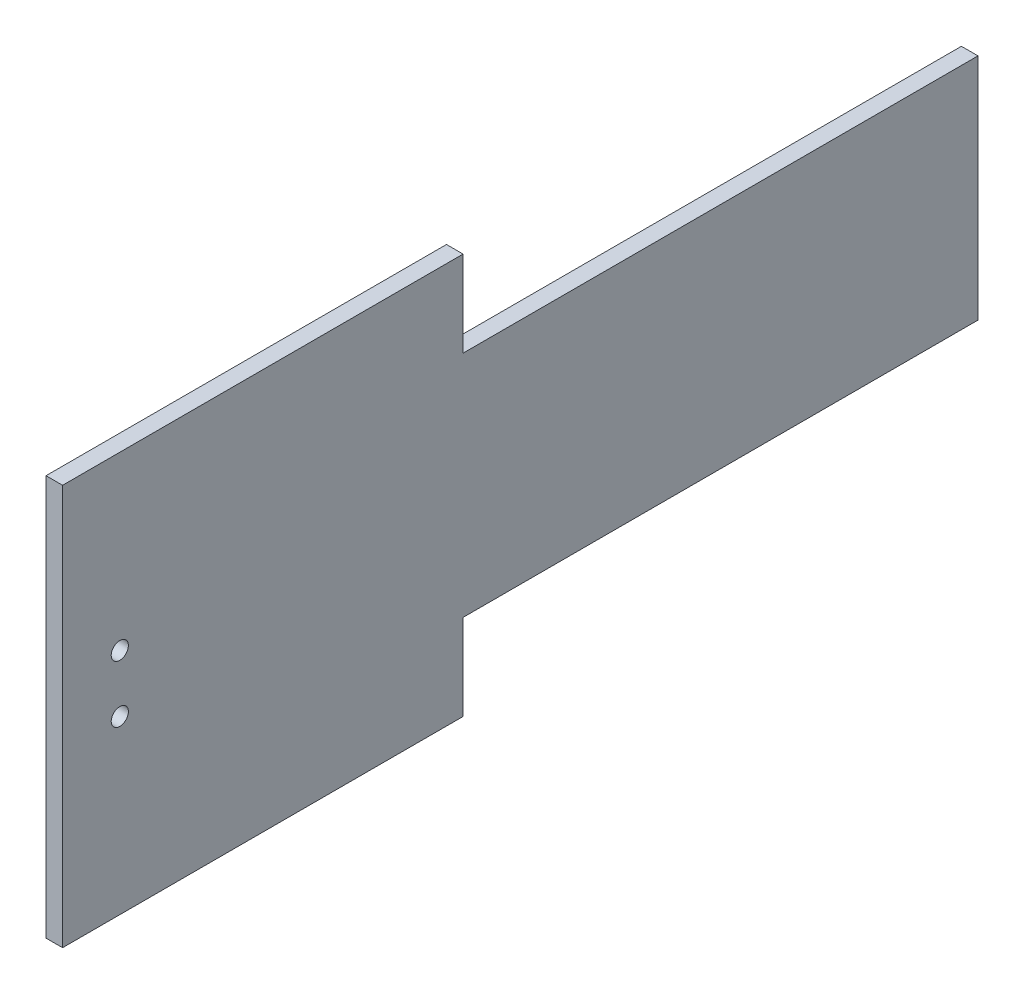
SolidWorks part; units mm, degrees
ref_plane "Front Plane" through (0, 0, 0) normal (0, 0, 1) x (1, 0, 0)
ref_plane "Top Plane" through (0, 0, 0) normal (0, 1, 0) x (1, 0, 0)
ref_plane "Right Plane" through (0, 0, 0) normal (1, 0, 0) x (0, 0, -1)
sketch "Sketch1" plane through (0, 0, 0) normal (1, 0, 0) x (0, 0, -1)
  line L0 (0, 0) -> (35, 0) construction
  line L1 (-35, 35) -> (35, 35)
  line L2 (-35, 35) -> (-35, -35)
  line L3 (-35, -35) -> (35, -35)
  line L4 (35, 35) -> (35, 20)
  line L5 (-35, 35) -> (35, -35) construction
  line L6 (-35, -35) -> (35, 35) construction
  line L7 (125, -20) -> (35, -20)
  line L8 (125, -20) -> (125, 20)
  line L9 (125, 20) -> (35, 20)
  line L11 (125, -20) -> (35, 20) construction
  line L12 (125, 20) -> (35, -20) construction
  line L13 (-35, -2.6865) -> (-25, -2.6865) construction
  line L14 (-25, -2.6865) -> (-25, 2.2551) construction
  line L15 (35, -20) -> (35, -35)
  line L16 (80, 0) -> (160, 0) construction
  circle A0 centre (-25, 5) radius 1.5
  circle A1 centre (-25, -5) radius 1.5
  point P0 (0, 0)
  point P6 (80, 0)
  point P21 (0, 0)
  dimension "D7" = 3
  dimension "D1" = 70
  dimension "D2" = 70
  dimension "D3" = 40
  dimension "D4" = 90
  dimension "D5" = 0
  dimension "D6" = 10
  dimension "D8" = 5
  dimension "D9" = 5
extrude "Boss-Extrude1" add sketch "Sketch1" along normal blind 2.9
